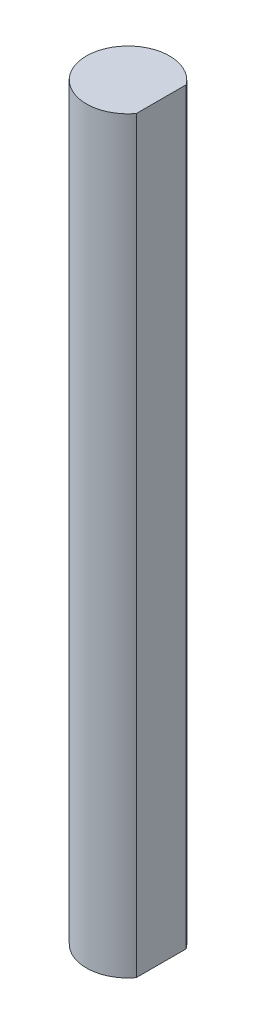
SolidWorks part; units mm, degrees
ref_plane "Front Plane" through (0, 0, 0) normal (0, 0, 1) x (1, 0, 0)
ref_plane "Top Plane" through (0, 0, 0) normal (0, 1, 0) x (1, 0, 0)
ref_plane "Right Plane" through (0, 0, 0) normal (1, 0, 0) x (0, 0, -1)
sketch "Sketch1" plane through (0, 0, 0) normal (0, 1, 0) x (1, 0, 0)
  line L0 (0, 0) -> (2.54, 0) construction
  line L1 (2.54, 3.81) -> (2.54, -3.81)
  circle A0 centre (0, 0) radius 3.175
  point P6 (2.54, 0)
  dimension "D1" = 6.35
  dimension "D2" = 2.54
  dimension "D3" = 7.62
extrude "Boss-Extrude1" add sketch "Sketch1" along normal blind 57.15
equation "\"D2@Sketch1\"=.125-.025"
